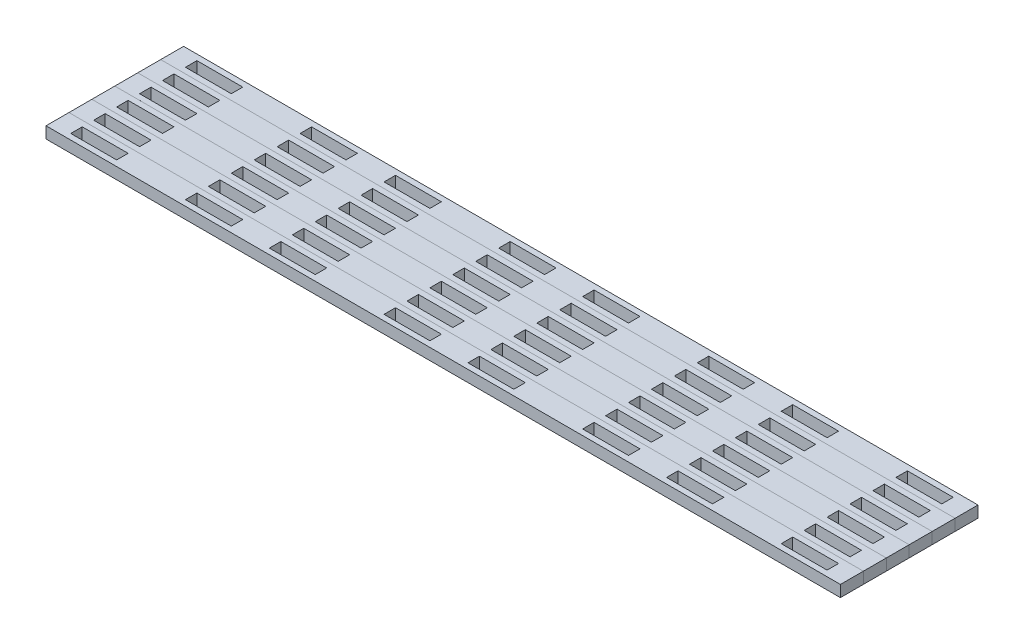
SolidWorks part; units mm, degrees
material "Cedar"
ref_plane "Front Plane" through (0, 0, 0) normal (0, 0, 1) x (1, 0, 0)
ref_plane "Top Plane" through (0, 0, 0) normal (0, 1, 0) x (1, 0, 0)
ref_plane "Right Plane" through (0, 0, 0) normal (1, 0, 0) x (0, 0, -1)
sketch "Sketch1" plane through (0, 0, 0) normal (0, 1, 0) x (1, 0, 0)
  line L1 (-219.9705, 6.35) -> (219.9705, 6.35)
  line L2 (-219.9705, 6.35) -> (-219.9705, -6.35)
  line L3 (-219.9705, -6.35) -> (219.9705, -6.35)
  line L4 (219.9705, 6.35) -> (219.9705, -6.35)
  line L5 (-219.9705, 6.35) -> (219.9705, -6.35) construction
  line L6 (-219.9705, -6.35) -> (219.9705, 6.35) construction
  point P0 (0, 0)
  dimension "D1" = 439.9409
  dimension "D2" = 12.7
extrude "Boss-Extrude1" add sketch "Sketch1" along normal blind 6.35
sketch "Sketch2" plane through (0, 6.35, 0) normal (0, 1, 0) x (1, 0, 0)
  line L0 (-23.2426, 0) -> (23.2426, 0) construction
  line L1 (-35.9426, 3.175) -> (-10.5426, 3.175)
  line L2 (-35.9426, 3.175) -> (-35.9426, -3.175)
  line L3 (-35.9426, -3.175) -> (-10.5426, -3.175)
  line L4 (-10.5426, 3.175) -> (-10.5426, -3.175)
  line L5 (-35.9426, 3.175) -> (-10.5426, -3.175) construction
  line L6 (-35.9426, -3.175) -> (-10.5426, 3.175) construction
  line L7 (10.5426, 3.175) -> (35.9426, 3.175)
  line L8 (10.5426, 3.175) -> (10.5426, -3.175)
  line L9 (10.5426, -3.175) -> (35.9426, -3.175)
  line L10 (35.9426, 3.175) -> (35.9426, -3.175)
  line L11 (10.5426, 3.175) -> (35.9426, -3.175) construction
  line L12 (10.5426, -3.175) -> (35.9426, 3.175) construction
  line L13 (-74.0426, 0) -> (-35.9426, 0) construction
  line L14 (-99.4426, 3.175) -> (-74.0426, 3.175)
  line L15 (-99.4426, 3.175) -> (-99.4426, -3.175)
  line L16 (-99.4426, -3.175) -> (-74.0426, -3.175)
  line L17 (-74.0426, 3.175) -> (-74.0426, -3.175)
  line L18 (-99.4426, 3.175) -> (-74.0426, -3.175) construction
  line L19 (-99.4426, -3.175) -> (-74.0426, 3.175) construction
  line L20 (74.0426, 3.175) -> (99.4426, 3.175)
  line L21 (74.0426, 3.175) -> (74.0426, -3.175)
  line L22 (74.0426, -3.175) -> (99.4426, -3.175)
  line L23 (99.4426, 3.175) -> (99.4426, -3.175)
  line L24 (74.0426, 3.175) -> (99.4426, -3.175) construction
  line L25 (74.0426, -3.175) -> (99.4426, 3.175) construction
  line L26 (35.9426, 0) -> (74.0426, 0) construction
  point P0 (-23.2426, 0)
  point P5 (23.2426, 0)
  point P12 (0, 0)
  point P13 (86.7426, 0)
  point P16 (-86.7426, 0)
  dimension "D1" = 46.4852
  dimension "D2" = 25.4
  dimension "D3" = 25.4
  dimension "D4" = 6.35
  dimension "D5" = 6.35
  dimension "D6" = 6.35
  dimension "D7" = 25.4
  dimension "D8" = 38.1
  dimension "D9" = 25.4
  dimension "D10" = 6.35
  dimension "D11" = 38.1
extrude "Cut-Extrude1" cut sketch "Sketch2" against normal through all
pattern_linear "LPattern1" count 2 spacing 219.9705 along (1, 0, 0) count 2 spacing 219.9705 along (-1, 0, 0) of "Cut-Extrude1"
pattern_linear "LPattern2" count 6 spacing 12.7 along (0, 0, 1) of bodies 103
